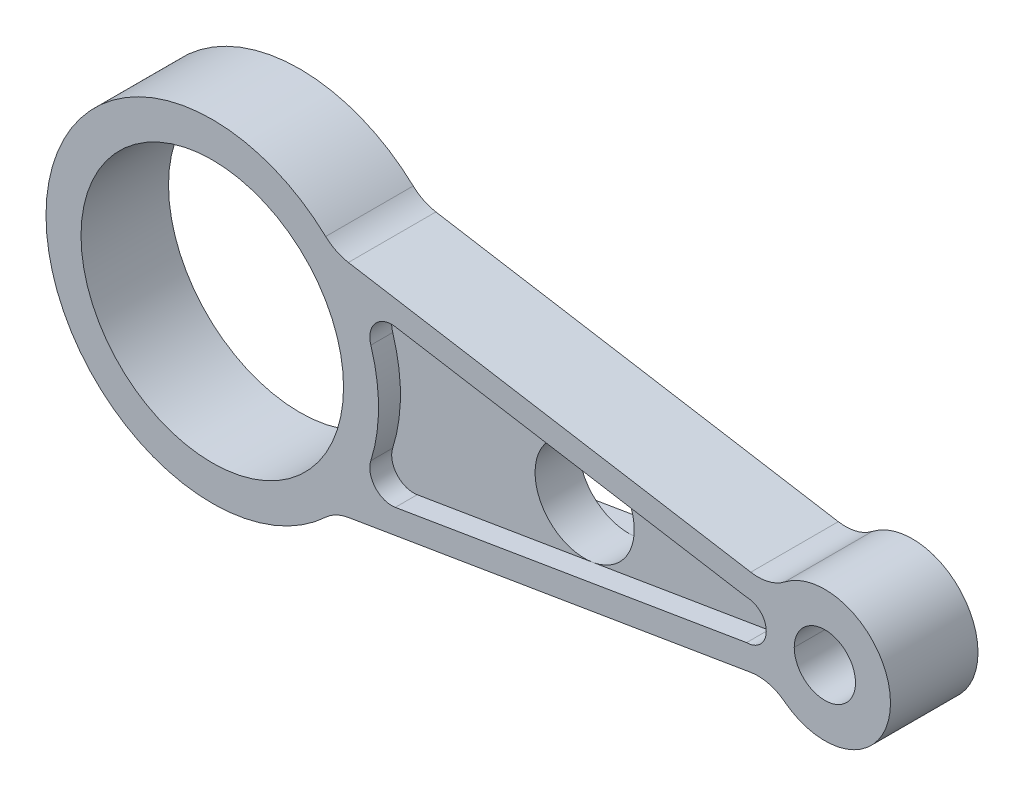
SolidWorks part; units mm, degrees
material "Plain Carbon Steel"
ref_plane "Front Plane" through (0, 0, 0) normal (0, 0, 1) x (1, 0, 0)
ref_plane "Top Plane" through (0, 0, 0) normal (0, 1, 0) x (1, 0, 0)
ref_plane "Right Plane" through (0, 0, 0) normal (1, 0, 0) x (0, 0, -1)
sketch "Sketch1" plane through (0, 0, 0) normal (0, 0, 1) x (1, 0, 0)
  line L0 (0, 0) -> (140, 0) construction
  line L1 (128.0638, 9.0844) -> (27.9355, 25.7606)
  line L2 (27.9355, -25.7606) -> (128.0638, -9.0844)
  circle A0 centre (0, 0) radius 30
  circle A1 centre (140, 0) radius 7
  arc A2 (27.9355, 25.7606) -> (27.9355, -25.7606) centre (0, 0) ccw
  arc A3 (128.0638, -9.0844) -> (128.0638, 9.0844) centre (140, 0) ccw
  arc A4 (38, 0) -> (27.9355, 25.7606) centre (0, 0) ccw construction
  arc A5 (27.9355, -25.7606) -> (38, 0) centre (0, 0) ccw construction
  arc A6 (128.0638, 9.0844) -> (125, 0) centre (140, 0) ccw construction
  arc A7 (125, 0) -> (128.0638, -9.0844) centre (140, 0) ccw construction
  dimension "D1" = 60
  dimension "D2" = 14
  dimension "D3" = 76
  dimension "D4" = 30
  dimension "D5" = 140
extrude "Boss-Extrude1" add sketch "Sketch1" along normal mid plane 20
fillet "Fillet1" radius 10 2 edges at (27.9355, 25.7606, 0) (27.9355, -25.7606, 0)
fillet "Fillet3" radius 10 2 edges at (128.0638, 9.0844, 0) (128.0638, -9.0844, 0)
sketch "Sketch2" plane through (0, 0, 10) normal (0, 0, 1) x (1, 0, 0)
  line L0 (0, 0) -> (140, 0) construction
  line L1 (41.8286, 17.871) -> (122.1113, 4.5)
  line L2 (41.8286, -17.871) -> (122.1113, -4.5)
  line L3 (123.0688, 9.9163) -> (31.1011, 25.2334) construction
  line L4 (31.1011, -25.2334) -> (123.0688, -9.9163) construction
  arc A0 (122.1113, -4.5) -> (122.1113, 4.5) centre (122.1113, 0) ccw
  arc A1 (41.8286, 17.871) -> (36.2389, 11.4344) centre (41.0071, 12.9389) ccw
  arc A2 (36.2389, 11.4344) -> (36.2389, -11.4344) centre (0, 0) cw
  arc A3 (36.2389, -11.4344) -> (41.8286, -17.871) centre (41.0071, -12.9389) ccw
  circle A4 centre (0, 0) radius 30 construction
  dimension "D3" = 4.5
  dimension "D4" = 5
  dimension "D5" = 8
  dimension "D1" = 5.5
  dimension "D2" = 5.5
extrude "Cut-Extrude1" cut sketch "Sketch2" against normal blind 5
mirror "Mirror1" about plane through (0, 0, 0) normal (0, 0, 1) of "Cut-Extrude1"
split line "Split Line1"
sketch "Sketch12" plane through (0, 0, 0) normal (0, 0, 1) x (1, 0, 0)
  line L0 (0, 0) -> (140, 0) construction
  line L1 (41.8286, 17.871) -> (122.1113, 4.5)
  line L2 (41.8286, -17.871) -> (122.1113, -4.5)
  line L3 (123.0688, 9.9163) -> (31.1011, 25.2334) construction
  line L4 (31.1011, -25.2334) -> (123.0688, -9.9163) construction
  arc A0 (122.1113, -4.5) -> (122.1113, 4.5) centre (122.1113, 0) ccw
  arc A1 (41.8286, 17.871) -> (36.2389, 11.4344) centre (41.0071, 12.9389) ccw
  arc A2 (36.2389, 11.4344) -> (36.2389, -11.4344) centre (0, 0) cw
  arc A3 (36.2389, -11.4344) -> (41.8286, -17.871) centre (41.0071, -12.9389) ccw
  circle A4 centre (80.107, 0) radius 11.3396
  circle A5 centre (0, 0) radius 30 construction
  point P16 (81.9699, 11.1855)
  dimension "D3" = 4.5
  dimension "D4" = 5
  dimension "D1" = 8
  dimension "D2" = 5.5
extrude "Cut-Extrude3" cut sketch "Sketch12" against normal through all from surface at 10 contours A4 starting at face at (140, 0, 10)
